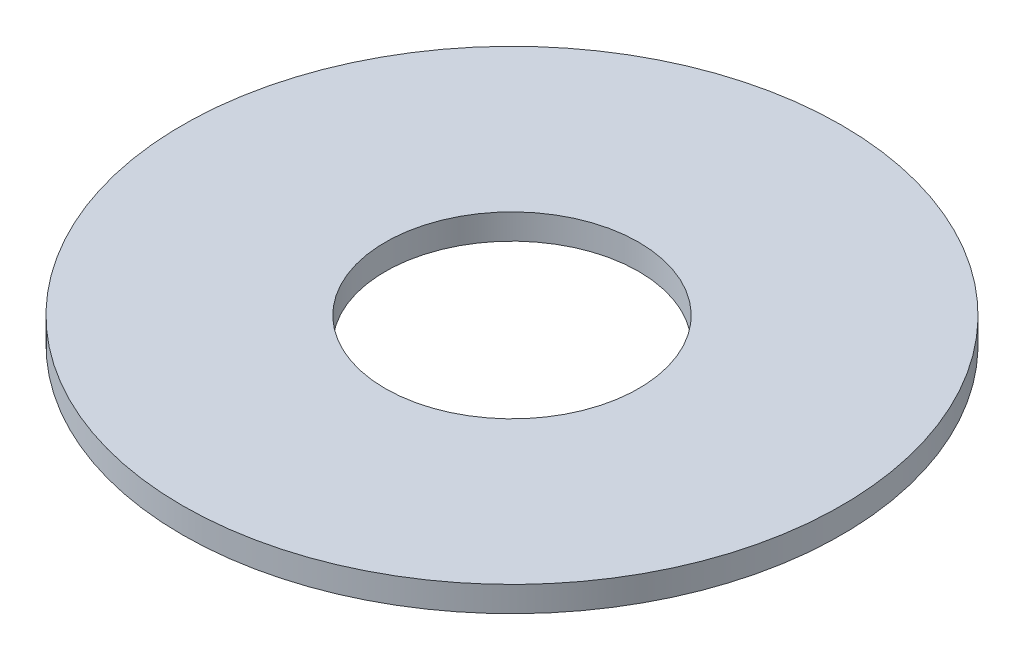
SolidWorks part; units mm, degrees
ref_plane "Front Plane" through (0, 0, 0) normal (0, 0, 1) x (1, 0, 0)
ref_plane "Top Plane" through (0, 0, 0) normal (0, 1, 0) x (1, 0, 0)
ref_plane "Right Plane" through (0, 0, 0) normal (1, 0, 0) x (0, 0, -1)
sketch "Sketch1" plane through (0, 0, 0) normal (0, 1, 0) x (1, 0, 0)
  line L0 (0, 15.875) -> (0, 41.275) construction
  circle A0 centre (0, 0) radius 15.875
  circle A1 centre (0, 0) radius 41.275
extrude "Boss-Extrude1" add sketch "Sketch1" along normal blind 3.175
